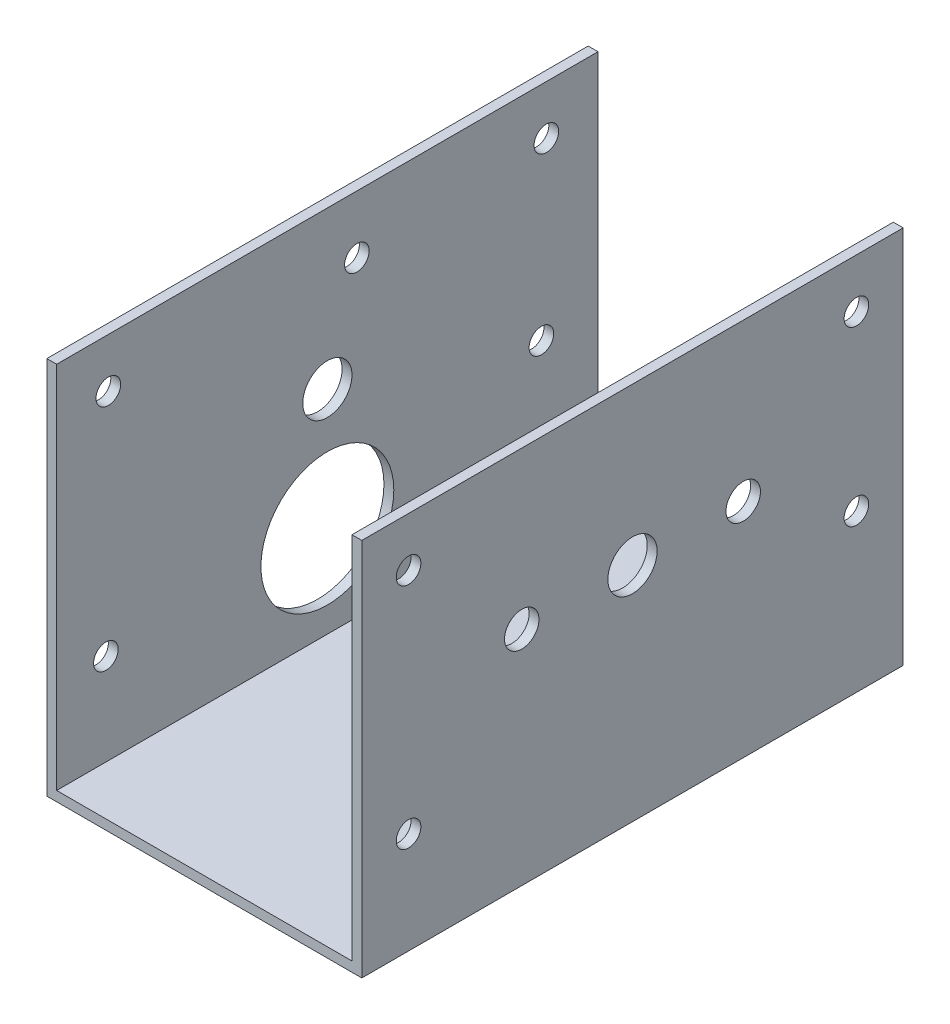
SolidWorks part; units mm, degrees
material "Liga 1060"
ref_plane "Plano frontal" through (0, 0, 0) normal (0, 0, 1) x (1, 0, 0)
ref_plane "Plano superior" through (0, 0, 0) normal (0, 1, 0) x (1, 0, 0)
ref_plane "Plano direito" through (0, 0, 0) normal (1, 0, 0) x (0, 0, -1)
sketch "Esboço1" plane through (0, 0, 0) normal (0, 1, 0) x (1, 0, 0)
  line L1 (30, -55) -> (-30, -55)
  line L2 (30, -55) -> (30, 55)
  line L3 (30, 55) -> (-30, 55)
  line L4 (-30, -55) -> (-30, 55)
  line L5 (30, -55) -> (-30, 55) construction
  line L6 (30, 55) -> (-30, -55) construction
  circle A0 centre (0, 0) radius 25
  point P0 (0, 0)
  dimension "D1" = 50
  dimension "D2" = 110
  dimension "D3" = 60
extrude "Ressalto-extrusão1" add sketch "Esboço1" along normal blind 2 contours A0 | L4 L1 L2 L3 A0
sketch "Esboço2" plane through (-30, 0, 0) normal (-1, 0, 0) x (0, 0, 1)
  line L0 (55, 2) -> (55, 0) construction
  line L1 (-55, 0) -> (55, 0)
  line L2 (-55, 0) -> (-55, 77)
  line L3 (-55, 77) -> (55, 77)
  line L4 (55, 0) -> (55, 77)
  dimension "D1" = 77
extrude "Ressalto-extrusão2" add sketch "Esboço2" along normal blind 2
mirror "Espelhar1" about plane through (0, 0, 0) normal (1, 0, 0) of "Ressalto-extrusão2"
sketch "Esboço3" plane through (0, 0, 0) normal (0, -1, 0) x (1, 0, 0)
  circle A0 centre (0, 0) radius 25
  dimension "D1" = 50
sketch "Esboço5" plane through (-30, 0, 0) normal (1, 0, 0) x (0, 0, -1)
  circle A0 centre (0, 20.625) radius 1 construction
  circle A1 centre (0, 20.625) radius 1
  circle A2 centre (0, 20.625) radius 13.5
  dimension "D1" = 27
extrude "Corte-extrusão3" cut sketch "Esboço5" against normal blind 10 contours A2 A1 | A1
sketch "Esboço6" plane through (-32, 0, 0) normal (-1, 0, 0) x (0, 0, 1)
  circle A0 centre (45, 20.625) radius 2.5 construction
  circle A1 centre (-6, 65.225) radius 2.5 construction
  circle A2 centre (-43.5, 31.925) radius 2.5 construction
  circle A3 centre (45, 20.625) radius 2.5
  circle A4 centre (-6, 65.225) radius 2.5
  circle A5 centre (-43.5, 31.925) radius 2.5
extrude "Corte-extrusão4" cut sketch "Esboço6" against normal blind 10
sketch "Esboço8" plane through (-32, 0, 0) normal (-1, 0, 0) x (0, 0, 1)
  circle A0 centre (0, 45.125) radius 5
  circle A1 centre (0, 20.625) radius 13.5 construction
  point P5 (0, 20.625)
  dimension "D2" = 10
  dimension "D1" = 24.5
extrude "Corte-extrusão7" cut sketch "Esboço8" against normal through all both and the other way through all
sketch "Esboço9" plane through (0, 2, 0) normal (0, 1, 0) x (1, 0, 0)
  circle A0 centre (-8.8388, 8.8388) radius 2.5 construction
  circle A1 centre (-8.8388, -8.8388) radius 2.5 construction
  circle A2 centre (8.8388, 8.8388) radius 2.5 construction
  circle A3 centre (8.8388, -8.8388) radius 2.5 construction
  circle A4 centre (-8.8388, 8.8388) radius 2.5
  circle A5 centre (-8.8388, -8.8388) radius 2.5
  circle A6 centre (8.8388, 8.8388) radius 2.5
  circle A7 centre (8.8388, -8.8388) radius 2.5
extrude "Corte-extrusão8" cut sketch "Esboço9" against normal blind 10
sketch "Esboço11" plane through (32, 0, 0) normal (1, 0, 0) x (0, 0, -1)
  circle A0 centre (-45, 20.625) radius 2.5 construction
  circle A1 centre (-45, 20.625) radius 2.5
sketch "Esboço12" plane through (32, 0, 0) normal (1, 0, 0) x (0, 0, -1)
  line L0 (55, 77) -> (55, 0) construction
  line L1 (55, 0) -> (-55, 0) construction
  line L2 (-55, 0) -> (-55, 77) construction
  circle A2 centre (45.5, 31.925) radius 2.5
  circle A3 centre (-45.5, 20.625) radius 2.5
  dimension "D3" = 5
  dimension "D5" = 5
  dimension "D6" = 20.625
  dimension "D1" = 9.5
  dimension "D2" = 31.925
  dimension "D4" = 9.5
extrude "Corte-extrusão9" cut sketch "Esboço12" against normal blind 10
sketch "Esboço13" plane through (-32, 0, 0) normal (-1, 0, 0) x (0, 0, 1)
  line L0 (55, 77) -> (-55, 77) construction
  line L1 (-55, 77) -> (-55, 0) construction
  line L2 (0, -35.2) -> (0, 35.2) construction
  circle A0 centre (-44.5, 67) radius 2.5
  circle A1 centre (44.5, 67) radius 2.5
  dimension "D1" = 5
  dimension "D2" = 10
  dimension "D3" = 10.5
extrude "Corte-extrusão10" cut sketch "Esboço13" against normal up to next
sketch "Esboço15" plane through (32, 0, 0) normal (1, 0, 0) x (0, 0, -1)
  circle A0 centre (-22.5, 45.125) radius 3.5
  circle A1 centre (22.5, 45.125) radius 3.5
  circle A2 centre (0, 45.125) radius 5 construction
  dimension "D2" = 22.5
  dimension "D3" = 7
  dimension "D4" = 7
  dimension "D1" = 45
extrude "Corte-extrusão11" cut sketch "Esboço15" against normal blind 10
sketch "Sketch1" plane through (32, 0, 0) normal (1, 0, 0) x (0, 0, -1)
  line L0 (55, 77) -> (55, 0) construction
  line L1 (-55, 77) -> (55, 77) construction
  line L2 (0, 35.2) -> (0, -35.2) construction
  circle A0 centre (45.5, 67) radius 2.5
  circle A4 centre (-45.5, 67) radius 2.5
  point P4 (0, 0)
  dimension "D1" = 5
  dimension "D3" = 10
  dimension "D2" = 9.5
extrude "Cut-Extrude1" cut sketch "Sketch1" against normal up to next
